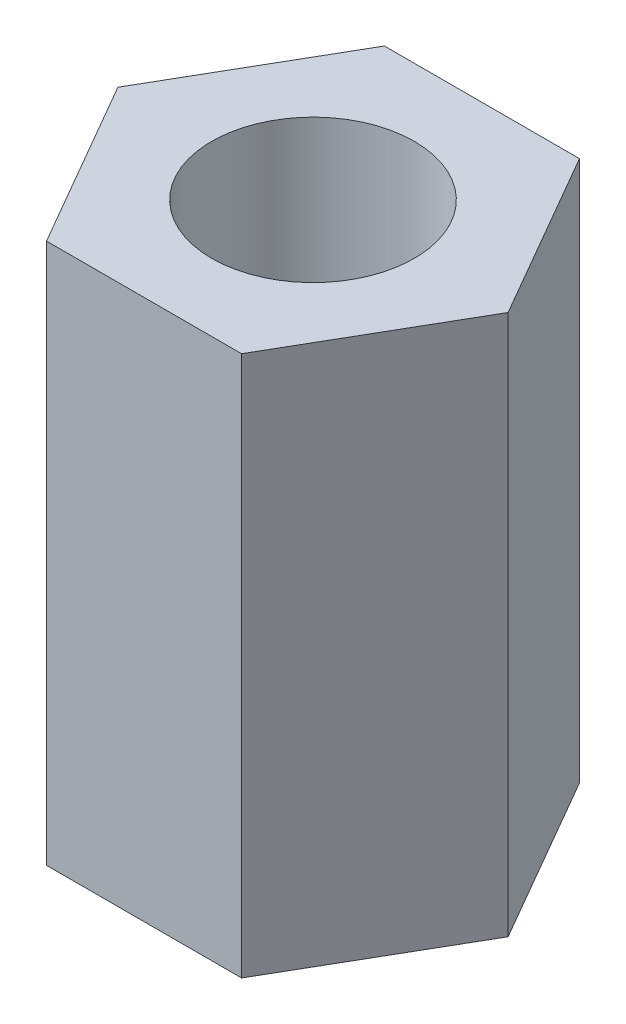
SolidWorks part; units mm, degrees
material "ABS"
ref_plane "Alzado" through (0, 0, 0) normal (0, 0, 1) x (1, 0, 0)
ref_plane "Planta" through (0, 0, 0) normal (0, 1, 0) x (1, 0, 0)
ref_plane "Vista lateral" through (0, 0, 0) normal (1, 0, 0) x (0, 0, -1)
sketch "Croquis1" plane through (0, 0, 0) normal (0, 1, 0) x (1, 0, 0)
  line L1 (1.4434, -2.5) -> (2.8868, 0)
  line L2 (2.8868, 0) -> (1.4434, 2.5)
  line L3 (1.4434, 2.5) -> (-1.4434, 2.5)
  line L4 (-1.4434, 2.5) -> (-2.8868, 0)
  line L5 (-2.8868, 0) -> (-1.4434, -2.5)
  line L6 (-1.4434, -2.5) -> (1.4434, -2.5)
  circle A0 centre (0, 0) radius 2.5 construction
  circle A1 centre (0, 0) radius 1.5
  dimension "D2" = 3
  dimension "D1" = 5
extrude "Saliente-Extruir1" add sketch "Croquis1" along normal mid plane 8
